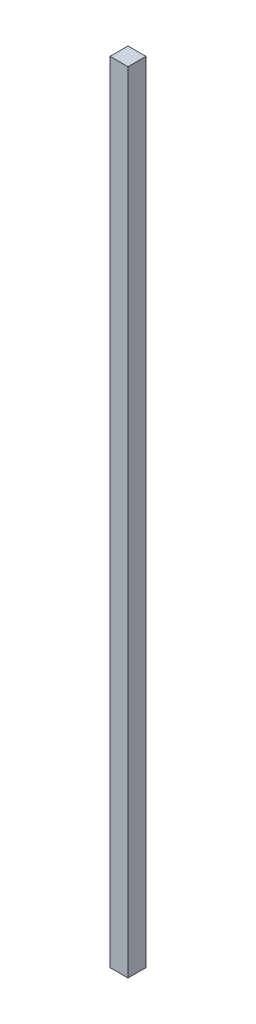
SolidWorks part; units mm, degrees
ref_plane "前视基准面" through (0, 0, 0) normal (0, 0, 1) x (1, 0, 0)
ref_plane "上视基准面" through (0, 0, 0) normal (0, 1, 0) x (1, 0, 0)
ref_plane "右视基准面" through (0, 0, 0) normal (1, 0, 0) x (0, 0, -1)
sketch "草图1" plane through (0, 0, 0) normal (0, 0, 1) x (1, 0, 0)
  line L1 (2.5, -110) -> (-2.5, -110)
  line L2 (2.5, -110) -> (2.5, 110)
  line L3 (2.5, 110) -> (-2.5, 110)
  line L4 (-2.5, -110) -> (-2.5, 110)
  line L5 (0, 110) -> (0, -110) construction
  line L6 (2.5, 0) -> (-2.5, 0) construction
  point P0 (0, 0)
  dimension "D1" = 5
  dimension "D2" = 220
extrude "凸台-拉伸1" add sketch "草图1" along normal blind 5
